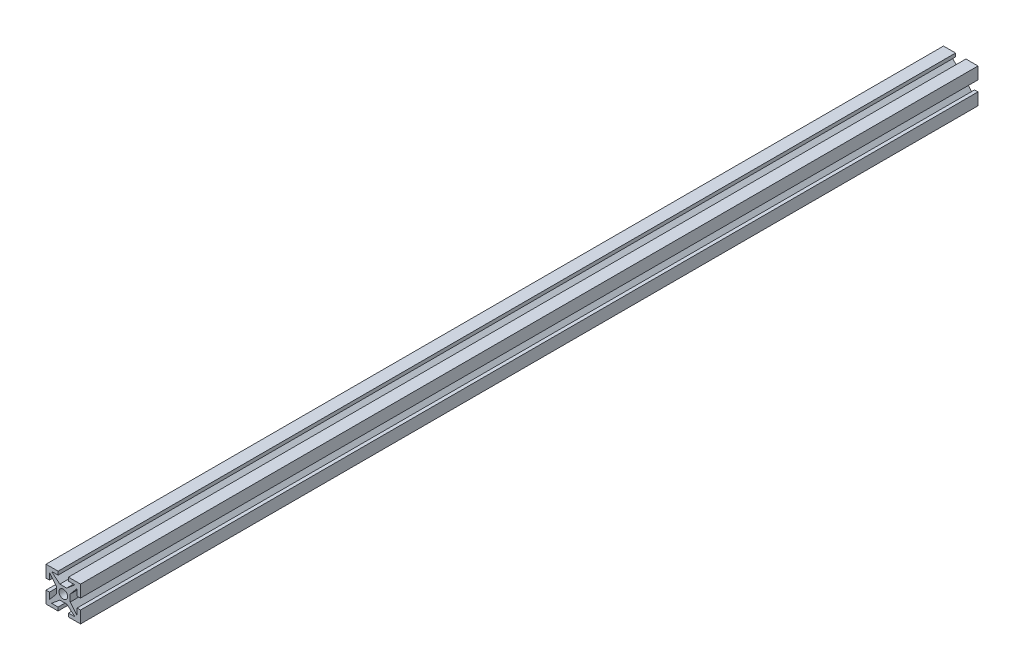
SolidWorks part; units mm, degrees
ref_plane "Front Plane" through (0, 0, 0) normal (0, 0, 1) x (1, 0, 0)
ref_plane "Top Plane" through (0, 0, 0) normal (0, 1, 0) x (1, 0, 0)
ref_plane "Right Plane" through (0, 0, 0) normal (1, 0, 0) x (0, 0, -1)
sketch "Esquisse2" plane through (0, 0, 0) normal (0, 0, 1) x (1, 0, 0)
  line L0 (-1, -2) -> (1, -2)
  line L1 (1, -2) -> (3.3835, -4)
  line L2 (3.3835, -4) -> (1.5, -4)
  line L3 (1.5, -4) -> (1.5, -5)
  line L4 (1.5, -5) -> (5, -5)
  line L5 (-1, -2) -> (-3.3835, -4)
  line L6 (-3.3835, -4) -> (-1.5, -4)
  line L7 (-1.5, -4) -> (-1.5, -5)
  line L8 (-1.5, -5) -> (-5, -5)
  line L9 (-5, -5) -> (-5, -1.5)
  line L10 (-5, -1.5) -> (-4, -1.5)
  line L11 (-4, -1.5) -> (-4, -3.3835)
  line L12 (-4, -3.3835) -> (-2, -1)
  line L13 (-2, -1) -> (-2, 1)
  line L14 (-2, 1) -> (-4, 3.3835)
  line L15 (-4, 3.3835) -> (-4, 1.5)
  line L16 (-4, 1.5) -> (-5, 1.5)
  line L17 (-5, 1.5) -> (-5, 5)
  line L18 (-5, 5) -> (-1.5, 5)
  line L19 (-1.5, 5) -> (-1.5, 4)
  line L20 (-1.5, 4) -> (-3.3835, 4)
  line L21 (-3.3835, 4) -> (-1, 2)
  line L22 (-1, 2) -> (1, 2)
  line L23 (1, 2) -> (3.3835, 4)
  line L24 (3.3835, 4) -> (1.5, 4)
  line L25 (1.5, 4) -> (1.5, 5)
  line L26 (1.5, 5) -> (5, 5)
  line L27 (5, 5) -> (5, 1.5)
  line L28 (5, 1.5) -> (4, 1.5)
  line L29 (4, 1.5) -> (4, 3.3835)
  line L30 (4, 3.3835) -> (2, 1)
  line L31 (2, -1) -> (2, 1)
  line L32 (2, -1) -> (4, -3.3835)
  line L33 (4, -3.3835) -> (4, -1.5)
  line L34 (4, -1.5) -> (5, -1.5)
  line L35 (5, -1.5) -> (5, -5)
  circle A0 centre (0, 0) radius 1.25
  point P4 (0, -2)
  point P34 (0, 2)
  point P40 (2, 0)
  dimension "D4" = 2.5
  dimension "D1" = 2
  dimension "D2" = 3.5
  dimension "D3" = 1
  dimension "D5" = 10
  dimension "D6" = 10
  dimension "D7" = 140
  dimension "D8" = 4
  dimension "D9" = 4
  dimension "D10" = 3.5
  dimension "D11" = 3
extrude "Main Extrusion" add sketch "Esquisse2" along normal blind 260
